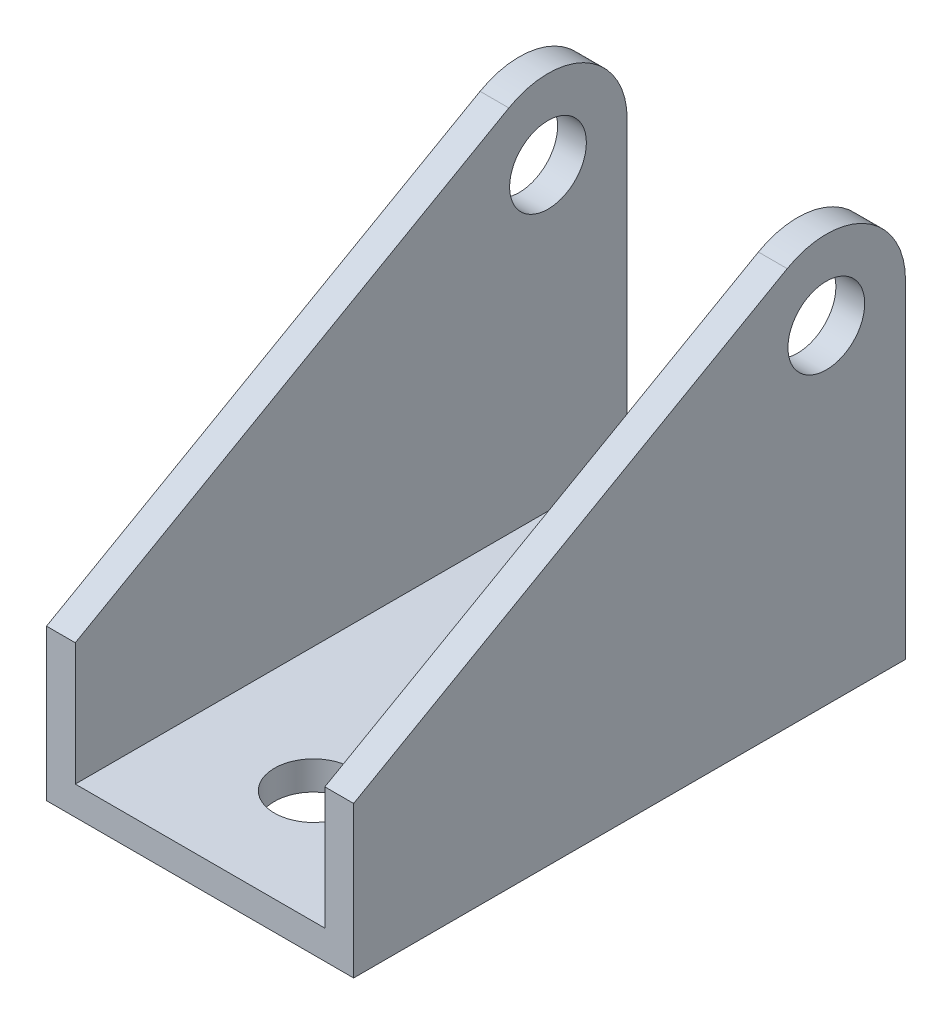
SolidWorks part; units mm, degrees
ref_plane "Front Plane" through (0, 0, 0) normal (0, 0, 1) x (1, 0, 0)
ref_plane "Top Plane" through (0, 0, 0) normal (0, 1, 0) x (1, 0, 0)
ref_plane "Right Plane" through (0, 0, 0) normal (1, 0, 0) x (0, 0, -1)
sketch "Sketch1" plane through (0, 0, 0) normal (1, 0, 0) x (0, 0, -1)
  line L0 (0, 16.002) -> (45.8965, 42.0854)
  line L1 (0, 0) -> (58.42, 0)
  line L2 (0, 0) -> (0, 16.002)
  line L4 (58.42, 0) -> (58.42, 34.798)
  arc A0 (58.42, 34.798) -> (45.8965, 42.0854) centre (50.038, 34.798) ccw
  circle A1 centre (50.038, 34.798) radius 4.064
  dimension "D3" = 16.764
  dimension "D2" = 8.128
  dimension "D1" = 58.42
  dimension "D4" = 16.002
extrude "Boss-Extrude1" add sketch "Sketch1" against normal blind 32.512
sketch "Sketch2" plane through (0, 0, 0) normal (0, 0, 1) x (1, 0, 0)
  line L0 (-32.512, 42.0854) -> (-32.512, 16.002) construction
  line L5 (-29.464, 3.048) -> (-3.048, 3.048)
  line L6 (-29.464, 3.048) -> (-29.464, 43.18)
  line L7 (-29.464, 43.18) -> (-3.048, 43.18)
  line L8 (-3.048, 3.048) -> (-3.048, 43.18)
  line L9 (0, 42.0854) -> (0, 16.002) construction
  line L10 (-32.512, 0) -> (0, 0) construction
  line L11 (0, 43.18) -> (-32.512, 43.18) construction
  dimension "D1" = 3.048
  dimension "D2" = 3.048
  dimension "D3" = 3.048
extrude "Cut-Extrude1" cut sketch "Sketch2" against normal through all
sketch "Sketch3" plane through (0, 0, 0) normal (0, 1, 0) x (1, 0, 0)
  line L1 (-20.574, 48.42) -> (-20.574, 58.42)
  line L2 (-29.464, 58.42) -> (-3.048, 58.42) construction
  line L3 (-11.938, 48.42) -> (-11.938, 58.42)
  line L4 (-20.574, 58.42) -> (-11.938, 58.42)
  line L5 (-16.256, 0) -> (-16.256, 58.42) construction
  line L6 (-32.512, 0) -> (0, 0) construction
  circle A0 centre (-16.256, 12) radius 4.125
  arc A1 (-20.574, 48.42) -> (-11.938, 48.42) centre (-16.256, 48.42) ccw
  dimension "D2" = 8.25
  dimension "D3" = 8.636
  dimension "D4" = 10
  dimension "D5" = 12
extrude "Cut-Extrude3" cut sketch "Sketch3" against normal blind 35.052 and the other way through all
